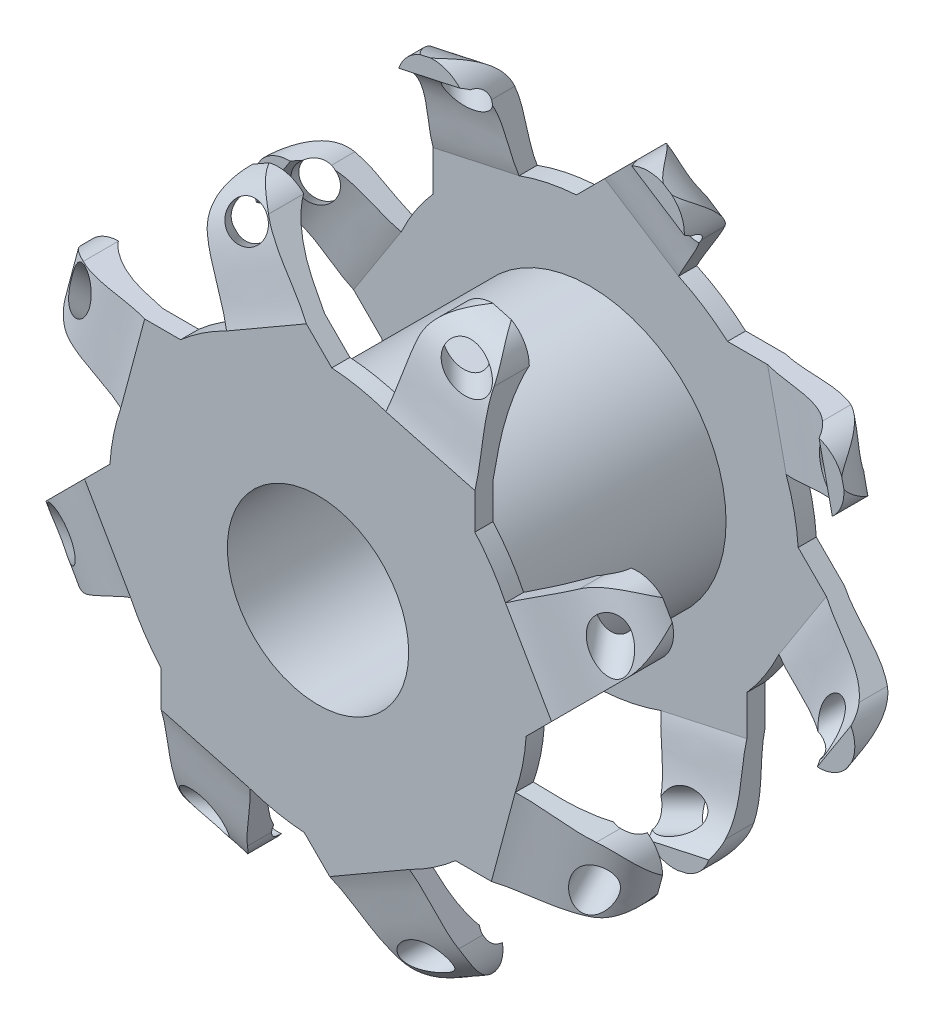
SolidWorks part; units mm, degrees
ref_plane "Front Plane" through (0, 0, 0) normal (0, 0, 1) x (1, 0, 0)
ref_plane "Top Plane" through (0, 0, 0) normal (0, 1, 0) x (1, 0, 0)
ref_plane "Right Plane" through (0, 0, 0) normal (1, 0, 0) x (0, 0, -1)
sketch "Sketch1" plane through (0, 0, 0) normal (0, 0, 1) x (1, 0, 0)
  circle A0 centre (0, 0) radius 15
extrude "ss-Extrude1" add sketch "Sketch1" against normal blind 30
sketch "Sketch2" plane through (0, 0, 0) normal (0, 0, 1) x (1, 0, 0)
  circle A0 centre (0, 0) radius 23
extrude "Boss-Extrude2" add sketch "Sketch2" along normal blind 2
sketch "Sketch3" plane through (0, 0, -30) normal (0, 0, -1) x (-1, 0, 0)
  circle A0 centre (0, 0) radius 23
extrude "Boss-Extrude3" add sketch "Sketch3" against normal blind 2
ref_plane "Plane1" through (28, 0, 0) normal (1, 0, 0) x (0, 0, -1)
sketch "Sketch4" plane through (28, 0, 0) normal (1, 0, 0) x (0, 0, -1)
  line L0 (0, 0) -> (14, 0)
  line L1 (14, 0) -> (30, 16.0781)
  line L2 (30, -23) -> (30, 23) construction
  line L3 (14, 0) -> (-2, -16.2079)
  line L4 (-2, 23) -> (-2, -23) construction
  line L5 (14, 0) -> (13.9236, 0.0764)
  line L6 (14, 0) -> (3.16, 10.84)
sketch "Sketch5" plane through (0, 0, 2) normal (0, 0, 1) x (1, 0, 0)
  line L0 (28, 0) -> (28, -16.2079) construction
  line L1 (28, -17.6) -> (28, 17.6) construction
  line L2 (28, -17.3013) -> (6.9558, -17.3013)
  line L3 (6.9558, -17.3013) -> (15.3256, -5.7668)
  line L4 (29.0346, -9.4374) -> (15.3256, -5.7668)
  arc A0 (28, -17.3013) -> (28, -9.3013) centre (28, -13.3013) ccw
extrude "Boss-Extrude4" add sketch "Sketch5" against normal blind 6
sketch "Sketch6" plane through (0, 0, -30) normal (0, 0, -1) x (-1, 0, 0)
  line L0 (-28, 0) -> (-28, 16.0781) construction
  line L1 (-28, 17.6) -> (-28, -17.6) construction
  line L2 (-28, 17.2961) -> (-10.1891, 17.2961)
  line L3 (-28.8479, 9.387) -> (-15.8212, 6.5615)
  line L4 (-15.8212, 6.5615) -> (-10.1891, 17.2961)
  arc A0 (-28, 17.2961) -> (-28, 9.2961) centre (-28, 13.2961) ccw
extrude "Boss-Extrude5" add sketch "Sketch6" against normal blind 6
ref_plane "Plane2" through (0, 7, -7) normal (0, 0.7071, -0.7071) x (0, 0.7071, 0.7071)
sketch "Sketch8" plane through (0, 7, -7) normal (0, 0.7071, -0.7071) x (0, 0.7071, 0.7071)
  circle A0 centre (-10.1867, 28.3313) radius 2
extrude "Cut-Extrude1" cut sketch "Sketch8" against normal through all and the other way through all
sketch "Sketch9" plane through (-0.4156, -1.5521, 0) normal (0.2586, 0.966, 0) x (0.966, -0.2586, 0)
  line L0 (22.9438, 0) -> (16.4364, 0)
  line L1 (16.4364, 0) -> (16.4364, 6.6211)
  line L2 (16.4364, 6.6211) -> (28.0515, 8.7622)
  line L3 (22.9438, 4) -> (22.9438, 0) construction
  line L4 (34.392, 4.3025) -> (35.0708, 7.8477)
  line L5 (35.0708, 7.8477) -> (40.0719, 2.3502)
  line L6 (40.0719, 2.3502) -> (38.1575, -7.6472)
  line L7 (38.1575, -7.6472) -> (19.1227, -3.4801)
  line L8 (19.1227, -3.4801) -> (22.9438, -2)
  spline S0 degree 3 poles (22.9438, 0) (25.0956, 0.4734) (30.0593, 1.469) (34.5835, 6.662) (28.0515, 8.7622) knots 0 0 0 0 0.412137 1 1 1 1
  spline S1 degree 3 poles (22.9438, -2) (27.0653, -0.6737) (33.5988, -1.518) (34.392, 4.3025) knots 0 0 0 0 1 1 1 1
  ellipse M1 centre (29.7594, 5.1571) end of major axis (29.0262, 7.9919) minor radius 2 (30.4875, 2.321) -> (28.0515, 4) cw
  line M2 (28.0515, 4) -> (22.9438, 4)
  line M3 (22.9438, 4) -> (22.9438, 0)
  line M5 (22.9438, -2) -> (30.4875, -2)
  line M6 (30.4875, -2) -> (30.4875, 2.321)
sketch "Sketch10" plane through (-0.6484, 2.9892, 0) normal (0.212, -0.9773, 0) x (0.9773, 0.212, 0)
  line L0 (32.5485, -23.1381) -> (18.6583, -21.4317)
  line L1 (18.6583, -21.4317) -> (17.2295, -28)
  line L2 (17.2295, -28) -> (22.7957, -28)
  line L3 (22.7957, -30) -> (17.9439, -31.9415)
  line L4 (17.9439, -31.9415) -> (39.3423, -33.3843)
  line L5 (39.3423, -33.3843) -> (34.3064, -17.9062)
  spline S0 degree 3 poles (22.7957, -28) (26.355, -26.9572) (31.0779, -27.8793) (32.5485, -23.1381) knots 0 0 0 0 1 1 1 1
  spline S1 degree 3 poles (22.7957, -30) (25.4358, -29.2716) (34.1516, -30.9557) (34.8971, -20.7314) (34.3064, -17.9062) knots 0 0 0 0 0.445444 1 1 1 1
  ellipse M1 centre (29.6535, -23.6812) end of major axis (30.2536, -26.5125) minor radius 2 (30.1821, -26.5257) -> (27.6778, -24) cw
  line M2 (27.6778, -24) -> (22.7957, -24)
  line M3 (22.7957, -24) -> (22.7957, -28)
  line M5 (22.7957, -30) -> (30.1821, -30)
  line M6 (30.1821, -30) -> (30.1821, -26.5257)
extrude "Cut-Extrude4" cut sketch "Sketch10" against normal blind 15 contours S0 L0 L1 L2 M1 M3 M2 | S0 M3 M1 M2 | S1 M5 M6 | S1 L3 L4 L5 M6 M5
extrude "Cut-Extrude5" cut sketch "Sketch9" against normal blind 15 contours S0 M3 M1 M2 | S0 L2 L1 L0 M1 M3 M2 | S1 L8 L7 L6 L5 L4 M6 M5 | S1 M5 M6
pattern_circular "CirPattern6" count 8 over 360 of "Boss-Extrude2", "Cut-Extrude1", "Boss-Extrude4", "Cut-Extrude5"
pattern_circular "CirPattern7" count 8 over 360 about axis through (0, 0, -30) along (0, 0, -1) of "Cut-Extrude4", "ss-Extrude1", "Cut-Extrude1", "Boss-Extrude5"
sketch "Sketch11" plane through (0, 0, 0) normal (0, 0, 1) x (1, 0, 0)
  circle A0 centre (0, 0) radius 10
extrude "Cut-Extrude6" cut sketch "Sketch11" against normal through all and the other way through all
